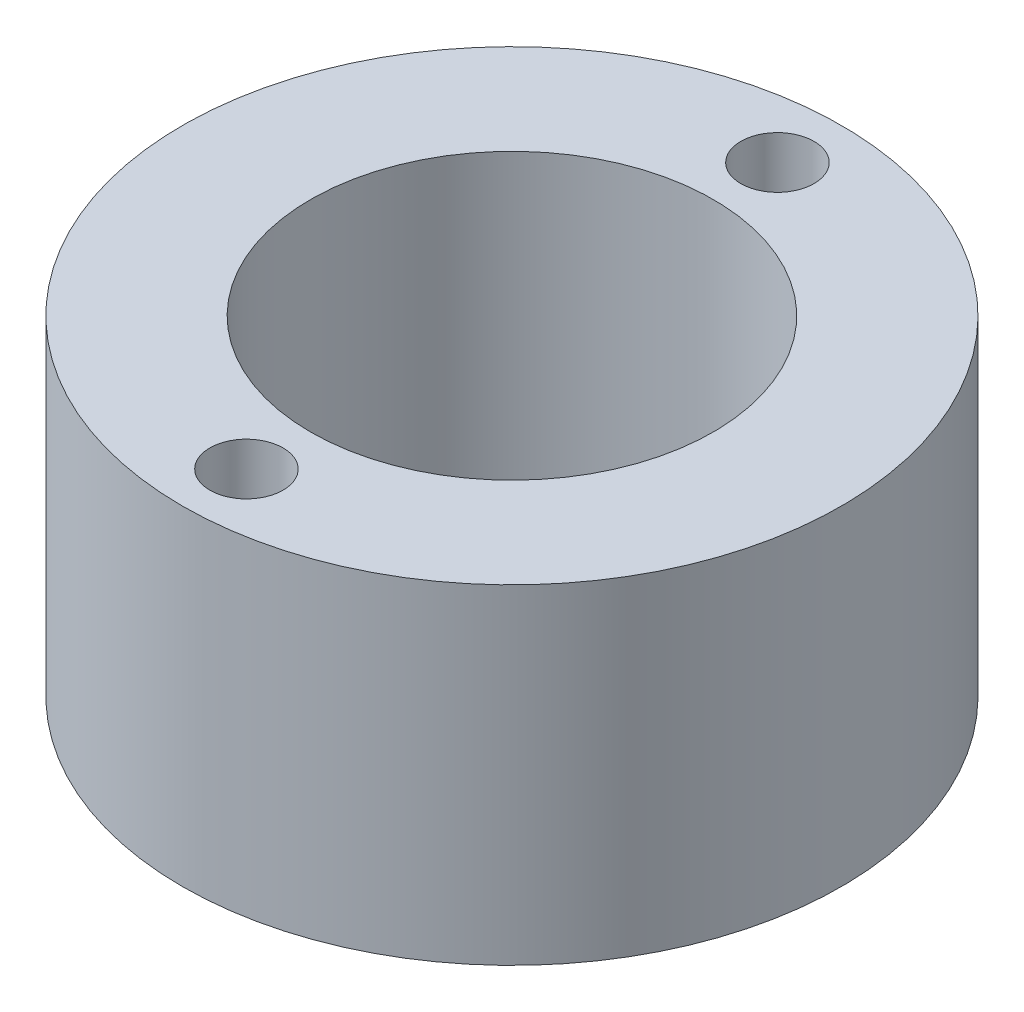
SolidWorks part; units mm, degrees
ref_plane "Front Plane" through (0, 0, 0) normal (0, 0, 1) x (1, 0, 0)
ref_plane "Top Plane" through (0, 0, 0) normal (0, 1, 0) x (1, 0, 0)
ref_plane "Right Plane" through (0, 0, 0) normal (1, 0, 0) x (0, 0, -1)
sketch "Sketch1" plane through (0, 0, 0) normal (0, 1, 0) x (1, 0, 0)
  circle A0 centre (0, 0) radius 6 construction
  circle A1 centre (0, 0) radius 9
  dimension "D1" = 12
  dimension "D2" = 3
extrude "Boss-Extrude1" add sketch "Sketch1" along normal blind 9 contours A1
sketch "Sketch2" plane through (0, 9, 0) normal (0, 1, 0) x (1, 0, 0)
  circle A0 centre (0, 0) radius 5.5
  dimension "D1" = 11
extrude "Cut-Extrude1" cut sketch "Sketch2" against normal blind 8
sketch "Sketch3" plane through (0, 9, 0) normal (0, 1, 0) x (1, 0, 0)
  line L0 (0, 5.5) -> (0, -9) construction
  line L1 (0, 5.5) -> (0, 9) construction
  line L2 (-9, 0) -> (9, 0) construction
  circle A0 centre (0, 0) radius 9 construction
  circle A1 centre (0, 0) radius 5.5 construction
  circle A2 centre (0, 0) radius 5.5 construction
  circle A3 centre (0, 7.25) radius 1
  circle A5 centre (0, -7.25) radius 1
  point P4 (0, -7.25)
  point P18 (0, 0)
  dimension "D1" = 2
extrude "Cut-Extrude2" cut sketch "Sketch3" against normal blind 3
